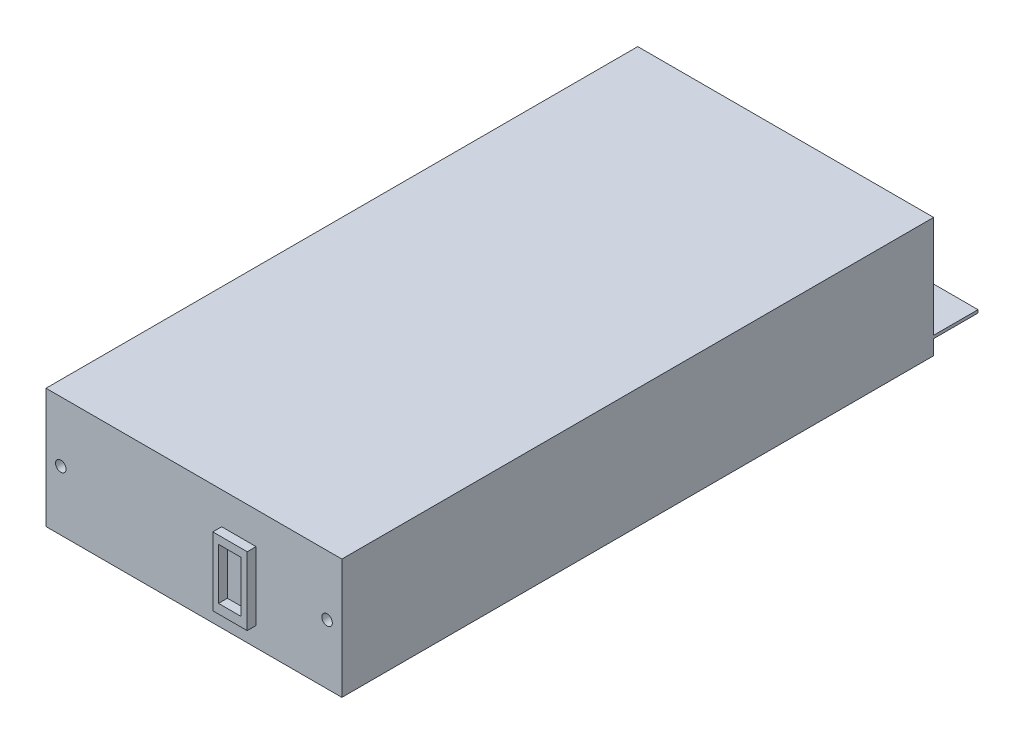
SolidWorks part; units mm, degrees
ref_plane "Front" through (0, 0, 0) normal (0, 0, 1) x (1, 0, 0)
ref_plane "Top" through (0, 0, 0) normal (0, 1, 0) x (1, 0, 0)
ref_plane "Right" through (0, 0, 0) normal (1, 0, 0) x (0, 0, -1)
sketch "Sketch1" plane through (0, 0, 0) normal (0, 0, 1) x (1, 0, 0)
  line L1 (0, 0) -> (100, 0)
  line L2 (0, 0) -> (0, -40.5)
  line L3 (0, -40.5) -> (100, -40.5)
  line L4 (100, 0) -> (100, -40.5)
  dimension "D1" = 40.5
  dimension "D2" = 100
extrude "Extrude1" add sketch "Sketch1" along normal blind 200
sketch "Sketch2" plane through (0, 0, 200) normal (0, 0, 1) x (1, 0, 0)
  line L0 (100, 0) -> (0, 0) construction
  line L1 (0, 0) -> (0, -40.5) construction
  circle A0 centre (95, -20.3) radius 1.778
  circle A1 centre (5, -20.3) radius 1.778
  dimension "D1" = 3.556
  dimension "D2" = 3.556
  dimension "D3" = 20.3
  dimension "D4" = 20.3
  dimension "D5" = 90
  dimension "D6" = 5
extrude "Cut-Extrude1" cut sketch "Sketch2" against normal blind 10
sketch "Sketch3" plane through (0, 0, 0) normal (0, 0, -1) x (-1, 0, 0)
  line L0 (-100, -40.5) -> (-100, 0) construction
  line L1 (0, -35.5) -> (-100, -35.5)
  line L2 (0, -35.5) -> (0, -34.5)
  line L3 (0, -34.5) -> (-100, -34.5)
  line L4 (-100, -35.5) -> (-100, -34.5)
  line L5 (0, -40.5) -> (-100, -40.5) construction
  line L6 (0, 0) -> (0, -40.5) construction
  dimension "D1" = 5
  dimension "D2" = 1
extrude "Extrude2" add sketch "Sketch3" along normal blind 15
sketch "Sketch4" plane through (0, -34.5, 0) normal (0, 1, 0) x (-1, 0, 0)
  line L0 (-100, 200) -> (0, 200) construction
  line L1 (-100, -15) -> (-100, 0) construction
  circle A0 centre (-15, -11) radius 1.778
  circle A1 centre (-85, -11) radius 1.778
  dimension "D1" = 3.556
  dimension "D2" = 3.556
  dimension "D3" = 70
  dimension "D4" = 211
  dimension "D5" = 15
extrude "Cut-Extrude2" cut sketch "Sketch4" against normal blind 15
sketch "Sketch5" plane through (0, 0, 200) normal (0, 0, 1) x (1, 0, 0)
  line L1 (71.0035, -10.8555) -> (59.3742, -10.8555)
  line L2 (71.0035, -10.8555) -> (71.0035, -33.953)
  line L3 (71.0035, -33.953) -> (59.3742, -33.953)
  line L4 (59.3742, -10.8555) -> (59.3742, -33.953)
extrude "Extrude3" add sketch "Sketch5" along normal blind 3
sketch "Sketch6" plane through (0, 0, 203) normal (0, 0, 1) x (1, 0, 0)
  line L1 (61.2994, -13.5303) -> (68.918, -13.5303)
  line L2 (61.2994, -13.5303) -> (61.2994, -30.8218)
  line L3 (61.2994, -30.8218) -> (68.918, -30.8218)
  line L4 (68.918, -13.5303) -> (68.918, -30.8218)
extrude "Cut-Extrude3" cut sketch "Sketch6" against normal blind 3
